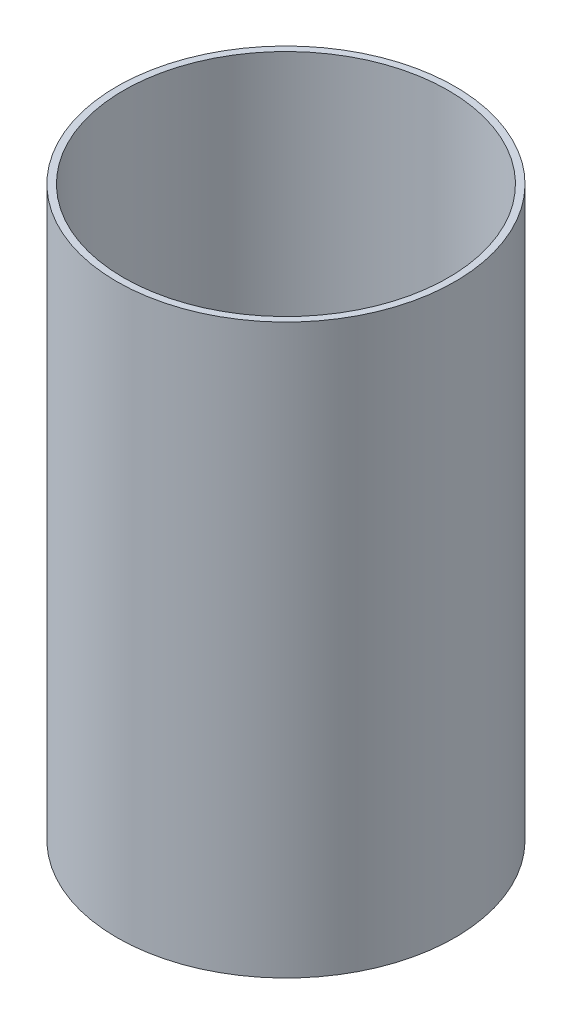
SolidWorks part; units mm, degrees
material "PTFE (general)"
ref_plane "Front Plane" through (0, 0, 0) normal (0, 0, 1) x (1, 0, 0)
ref_plane "Top Plane" through (0, 0, 0) normal (0, 1, 0) x (1, 0, 0)
ref_plane "Right Plane" through (0, 0, 0) normal (1, 0, 0) x (0, 0, -1)
ref_axis "Axis1" through (0, 55, 0) along (0, -1, 0)
sketch "Sketch2" plane through (0, 0, 0) normal (0, 0, 1) x (1, 0, 0)
  line L1 (-39.6875, 0) -> (-38.1, 0)
  line L2 (-39.6875, 0) -> (-39.6875, -133.35)
  line L3 (-39.6875, -133.35) -> (-38.1, -133.35)
  line L4 (-38.1, 0) -> (-38.1, -133.35)
  dimension "D2" = 1.5875
revolve "Revolve1" add sketch "Sketch2" angle 360 about axis through (0, 55, 0) along (0, -1, 0)
equation "\"D2@Sketch2\"=\"LINER THICKNESS@Cryo Tank.Assembly\""
